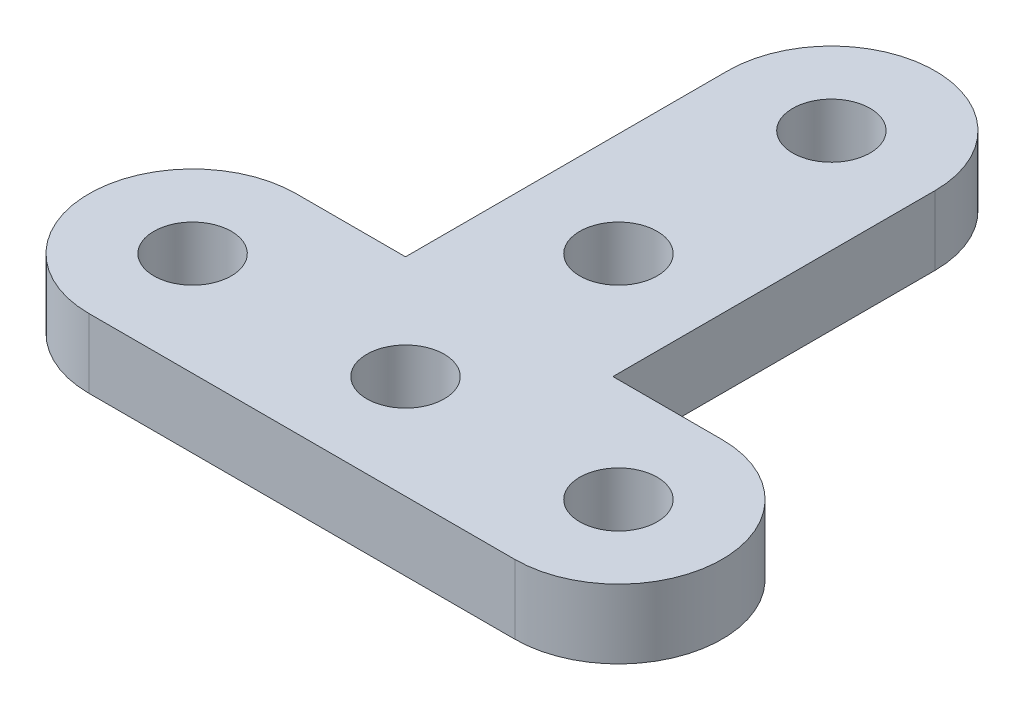
SolidWorks part; units mm, degrees
ref_plane "Front Plane" through (0, 0, 0) normal (0, 0, 1) x (1, 0, 0)
ref_plane "Top Plane" through (0, 0, 0) normal (0, 1, 0) x (1, 0, 0)
ref_plane "Right Plane" through (0, 0, 0) normal (1, 0, 0) x (0, 0, -1)
ref_plane "Plane1" through (0, 3.175, 0) normal (0, 1, 0) x (1, 0, 0)
sketch "Sketch1" plane through (0, 3.175, 0) normal (0, 1, 0) x (1, 0, 0)
  line L0 (4.7625, 4.7625) -> (4.7625, 19.558)
  line L1 (-4.7625, 19.558) -> (-4.7625, 4.7625)
  line L2 (-4.7625, 4.7625) -> (-9.779, 4.7625)
  line L3 (-9.779, -4.7625) -> (9.779, -4.7625)
  line L4 (9.779, 4.7625) -> (4.7625, 4.7625)
  circle A0 centre (0, 19.558) radius 1.778
  circle A1 centre (9.779, 0) radius 1.778
  arc A2 (4.7625, 19.558) -> (-4.7625, 19.558) centre (0, 19.558) ccw
  arc A3 (-9.779, 4.7625) -> (-9.779, -4.7625) centre (-9.779, 0) ccw
  arc A4 (9.779, -4.7625) -> (9.779, 4.7625) centre (9.779, 0) ccw
  circle A5 centre (0, 9.779) radius 1.778
  circle A6 centre (-9.779, 0) radius 1.778
  circle A7 centre (0, 0) radius 1.778
extrude "Boss-Extrude1" add sketch "Sketch1" against normal blind 3.175
